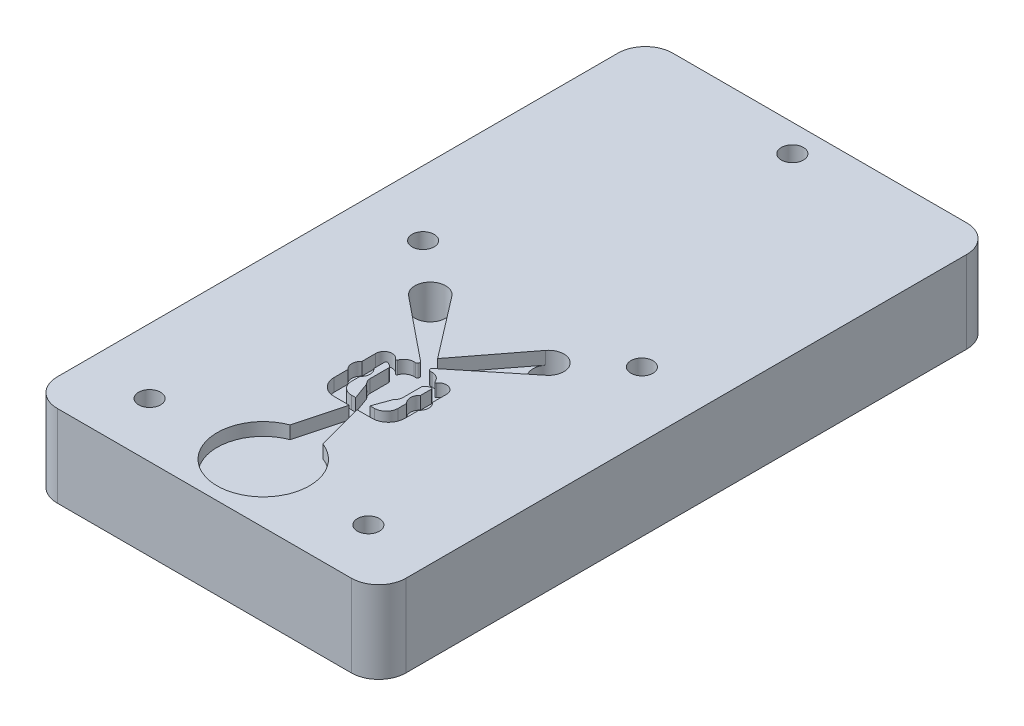
SolidWorks part; units mm, degrees
material "ABS"
ref_plane "Front Plane" through (0, 0, 0) normal (0, 0, 1) x (1, 0, 0)
ref_plane "Top Plane" through (0, 0, 0) normal (0, 1, 0) x (1, 0, 0)
ref_plane "Right Plane" through (0, 0, 0) normal (1, 0, 0) x (0, 0, -1)
sketch "Sketch1" plane through (0, 0, 0) normal (0, 1, 0) x (1, 0, 0)
  line L0 (142.353, -204.8394) -> (144.0267, -204.8394) construction
  line L1 (-1.1906, 0) -> (1.1906, 0) construction
  line L2 (0, 144.4498) -> (0, -46.0502) construction
  line L3 (-53.975, 144.4498) -> (53.975, 144.4498)
  line L4 (-53.975, 144.4498) -> (-53.975, -46.0502)
  line L5 (-53.975, -46.0502) -> (53.975, -46.0502)
  line L6 (53.975, 144.4498) -> (53.975, -46.0502)
  dimension "D1" = 2.3813
  dimension "D2" = 107.95
  dimension "D3" = 46.0502
  dimension "D4" = 190.5
sketch "Sketch2" plane through (0, 0, 0) normal (0, 1, 0) x (1, 0, 0)
  line L0 (-18.288, 42.1894) -> (18.288, 42.1894) construction
  line L1 (0, 144.4498) -> (0, -46.0502) construction
  line L2 (0, 42.1894) -> (0, -27.7953) construction
  line L3 (-53.975, -46.0502) -> (53.975, -46.0502) construction
  line L4 (1.1906, 0) -> (5.0579, -14.433)
  line L5 (1.1906, 0) -> (5.8805, 0)
  line L6 (10.9605, 5.08) -> (10.9605, 17.9832)
  line L7 (2.2225, 3.048) -> (4.1141, 8.245)
  line L8 (5.08, 10.3632) -> (5.08, 16.2674)
  line L9 (7.2267, 17.0349) -> (7.2267, 6.731)
  line L10 (2.2225, 3.048) -> (3.5437, 3.048)
  line L11 (0, 26.1793) -> (14.5097, 45.0886)
  line L12 (21.2851, 38.4882) -> (1.8864, 22.7794)
  line L13 (2.286, 21.651) -> (2.8194, 21.651)
  line L14 (0, 26.1793) -> (0, -42.0828)
  circle A1 centre (0, -27.7953) radius 14.2875
  arc A2 (5.8805, 0) -> (10.9605, 5.08) centre (5.8805, 5.08) ccw
  arc A3 (10.9605, 17.9832) -> (6.3753, 19.4894) centre (8.4205, 17.9832) ccw
  arc A4 (5.08, 16.2674) -> (6.7785, 17.4099) centre (7.2267, 14.9098) cw
  arc A5 (3.5437, 3.048) -> (7.2267, 6.731) centre (3.5437, 6.731) ccw
  arc A6 (5.08, 10.3632) -> (4.3016, 8.5334) centre (2.54, 10.3632) cw
  circle A7 centre (18.288, 42.1894) radius 4.7625
  arc A8 (2.8194, 21.651) -> (5.7995, 19.5713) centre (2.8194, 18.476) cw
  arc A9 (1.8864, 22.7794) -> (2.286, 21.651) centre (2.286, 22.286) ccw
  arc A10 (5.7995, 19.5713) -> (6.3753, 19.4894) centre (6.1094, 19.6852) ccw
  arc A11 (4.1141, 8.245) -> (4.3016, 8.5334) centre (4.8301, 7.9844) cw
  arc A12 (6.7785, 17.4099) -> (7.2267, 17.0349) centre (6.8457, 17.0349) cw
  point P4 (0, 42.1894)
  point P49 (7.2267, 17.4498)
  dimension "D2" = 28.575
  dimension "D6" = 5.08
  dimension "D7" = 2.54
  dimension "D12" = 3.7338
  dimension "D13" = 3.683
  dimension "D16" = 2.54
  dimension "D17" = 2.54
  dimension "D19" = 9.525
  dimension "D23" = 0.635
  dimension "D26" = 0.3302
  dimension "D27" = 3.175
  dimension "D29" = 0.762
  dimension "D30" = 0.381
  dimension "D1" = 27.7953
  dimension "D3" = 3.9674
  dimension "D4" = 15
  dimension "D5" = 4.6899
  dimension "D8" = 17.9832
  dimension "D9" = 3.048
  dimension "D10" = 20
  dimension "D11" = 4.445
  dimension "D14" = 10.16
  dimension "D15" = 17.4498
  dimension "D18" = 7.3152
  dimension "D20" = 36.576
  dimension "D21" = 42.1894
  dimension "D22" = 37.5
  dimension "D24" = 2.286
  dimension "D25" = 51
  dimension "D28" = 2.8194
  dimension "D31" = 3.8933
sketch "Sketch3" plane through (0, 0, 0) normal (0, 1, 0) x (1, 0, 0)
  line L0 (0, 144.4498) -> (0, -46.0502) construction
  line L1 (4.6237, 34.9454) -> (12.5222, -2.214)
  line L2 (-53.975, -46.0502) -> (53.975, -46.0502) construction
  line L3 (0, -42.5196) -> (0, 144.4498) construction
  line L4 (14.3423, 35.7124) -> (5.2449, 35.7124)
  line L5 (5.5801, 44.4119) -> (45.9235, 114.2888)
  line L6 (0, 61.8154) -> (22.9909, 124.9824)
  line L7 (0, 61.8154) -> (0, -42.5196)
  line L8 (-53.975, 144.4498) -> (53.975, 144.4498) construction
  line L9 (53.975, 144.4498) -> (53.975, -46.0502) construction
  circle A0 centre (0, -20.4216) radius 22.098
  arc A1 (5.2449, 35.7124) -> (4.6237, 34.9454) centre (5.2449, 35.0774) ccw
  circle A2 centre (18.288, 42.1894) radius 4.7625 construction
  circle A3 centre (18.288, 42.1894) radius 4.7625
  arc A4 (14.3423, 35.7124) -> (21.7695, 38.9397) centre (14.3423, 45.8724) ccw
  circle A5 centre (6.35, 43.9674) radius 0.889
  arc A6 (6.3117, 43.0792) -> (15.3752, 45.9573) centre (6.9087, 56.9093) ccw
  arc A12 (22.9909, 124.9824) -> (45.9235, 114.2888) centre (34.925, 120.6388) cw
  point P25 (0, 91.8403)
  point P26 (6.9087, 62.0362)
  point P27 (0, 64.068)
  point P28 (6.35, 44.8564)
  point P29 (5.9588, 44.7657)
  point P30 (24.5681, 94.0174)
  point P31 (28.6679, 103.4512)
  dimension "D3" = 44.196
  dimension "D7" = 0.635
  dimension "D8" = 10.16
  dimension "D9" = 1.778
  dimension "D12" = 13.843
  dimension "D13" = 69.85
  dimension "D14" = 17.848
  dimension "D27" = 12.7
  dimension "D28" = 11.111
  dimension "D29" = 6.35
  dimension "D1" = 20.4216
  dimension "D2" = 3.5306
  dimension "D4" = 12
  dimension "D5" = 25.0444
  dimension "D6" = 56.134
  dimension "D10" = 12.7
  dimension "D11" = 8.255
  dimension "D17" = 30
  dimension "D18" = 20
extrude "Boss-Extrude1" add sketch "Sketch1" along normal mid plane 25.4
extrude "Cut-Extrude1" cut sketch "Sketch2" against normal blind 3.9624 from surface at 12.7 contours A10 A8 L13 A9 L12 A7 L11 L14 A1 L4 L5 A2 L6 A3 A4 A12 L9 A5 L10 L7 A11 A6 L8 | A7 | L14 A1
extrude "Cut-Extrude2" cut sketch "Sketch3" along normal blind 14.6812 from surface at -12.7
sketch "Sketch5" plane through (0, 8.7376, 0) normal (0, 1, 0) x (1, 0, 0)
  circle A0 centre (18.288, 42.1894) radius 4.7625
  arc A1 (21.2851, 38.4882) -> (14.5097, 45.0886) centre (18.288, 42.1894) ccw construction
extrude "Cut-Extrude3" cut sketch "Sketch5" against normal through all
mirror "Mirror1" about plane through (0, 0, 0) normal (1, 0, 0) of "Cut-Extrude3", "Cut-Extrude2", "Cut-Extrude1"
scale "Scale1" scale about centroid uniform scaling yes scale factor 0.75
sketch "Sketch6" plane through (0, 9.7581, 0) normal (0, 1, 0) x (1, 0, 0)
  line L0 (-8.2204, 20.8982) -> (-5.42, 20.8982) construction
  line L1 (-8.2204, 25.7369) -> (-8.2204, 16.0595) construction
  line L2 (-5.42, 17.2978) -> (-5.42, 25.0257) construction
  line L5 (8.2204, 20.8982) -> (5.42, 20.8982) construction
  line L6 (8.2204, 25.7369) -> (8.2204, 16.0595) construction
  line L7 (5.42, 17.2978) -> (5.42, 25.0257) construction
  circle A0 centre (-6.8202, 20.8982) radius 2.1336
  circle A1 centre (6.8202, 20.8982) radius 2.1336
  dimension "D1" = 4.2672
extrude "Cut-Extrude4" cut sketch "Sketch6" against normal up to surface (2.9718 mm away) up to face at (0, 6.7863, -23.9115)
hole_wizard "#10 Clearance Hole1" positions "Sketch7" profile "Sketch8" hole size "#10" standard "ANSI Inch" end condition up to next
sketch "Sketch7" plane through (0, 9.7581, 0) normal (0, 1, 0) x (1, 0, 0)
  line L1 (-25.4, 53.9119) -> (25.4, 53.9119) construction
  line L2 (-25.4, 53.9119) -> (-25.4, -9.5881) construction
  line L3 (-25.4, -9.5881) -> (25.4, -9.5881) construction
  line L4 (25.4, 53.9119) -> (25.4, -9.5881) construction
  line L5 (0, 114.2369) -> (0, 53.9119) construction
  line L7 (40.4813, 120.5869) -> (-40.4812, 120.5869) construction
  line L8 (-40.4812, -22.2881) -> (40.4813, -22.2881) construction
  point P0 (0, 114.2369)
  point P2 (-25.4, 53.9119)
  point P4 (25.4, 53.9119)
  point P6 (25.4, -9.5881)
  point P8 (-25.4, -9.5881)
  dimension "D1" = 6.35
  dimension "D2" = 50.8
  dimension "D3" = 12.7
  dimension "D4" = 63.5
sketch "Sketch8" plane through (0, 9.7581, -114.2369) normal (1, 0, 0) x (0, 0, 1)
  line L0 (0, 0) -> (0, 19.05)
  line L1 (0, 19.05) -> (2.5527, 19.05)
  line L2 (2.5527, 19.05) -> (2.5527, 0)
  line L5 (2.5527, 0) -> (0, 0)
  line L11 (0, -6.35) -> (0, 107.95) construction
  dimension "Thru Hole Dia." = 5.1054
  dimension "Thru Hole Depth" = 19.05
fillet "Fillet1" radius 6.35 4 edges at (-40.4812, 0.2331, 22.2881) (-40.4812, 0.2331, -120.5869) (40.4813, 0.2331, -120.5869) (40.4813, 0.2331, 22.2881)
